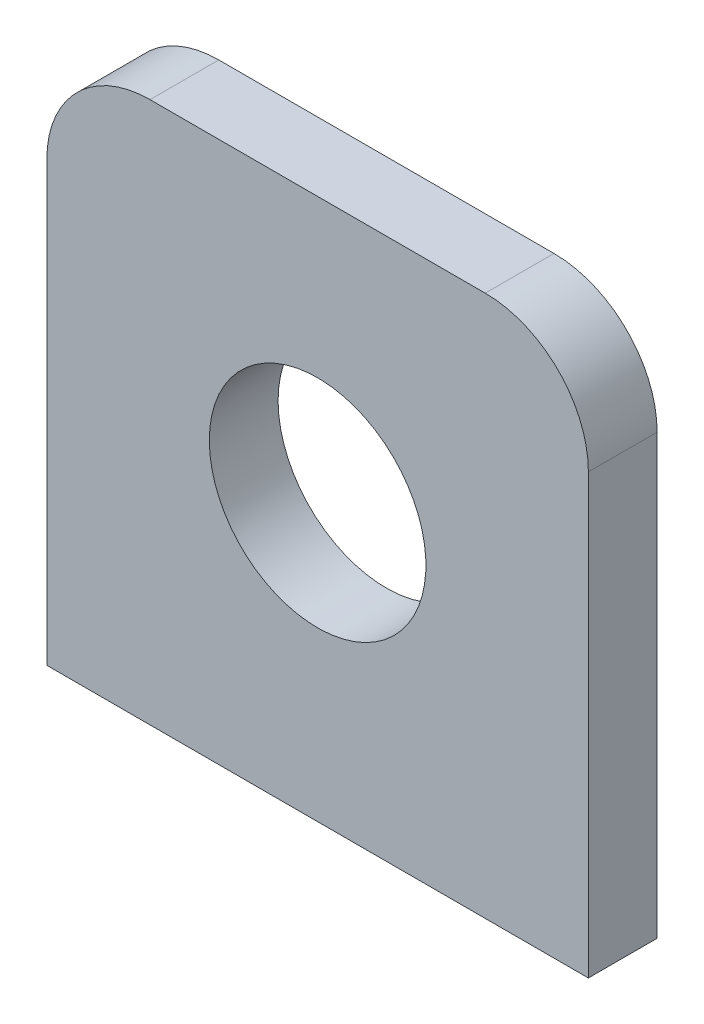
SolidWorks part; units mm, degrees
ref_plane "Plano frontal" through (0, 0, 0) normal (0, 0, 1) x (1, 0, 0)
ref_plane "Plano superior" through (0, 0, 0) normal (0, 1, 0) x (1, 0, 0)
ref_plane "Plano direito" through (0, 0, 0) normal (1, 0, 0) x (0, 0, -1)
ref_plane "Plano1" through (0, 0, 6.35) normal (0, 0, 1) x (1, 0, 0)
sketch "Esboço1" plane through (0, 0, 6.35) normal (0, 0, 1) x (1, 0, 0)
  line L0 (37, 0) -> (37, 50)
  line L1 (37, 50) -> (-13, 50)
  line L2 (-13, 50) -> (-13, 0)
  line L3 (-13, 0) -> (37, 0)
  dimension "D1" = 50
  dimension "D2" = 50
extrude "Ressalto-extrusão1" add sketch "Esboço1" against normal blind 6.35
hole_wizard "Furo com folga de M131" positions "Esboço5" profile "Esboço4" hole size "M13" standard "Ansi Metric" end condition through all
sketch "Esboço5" plane through (0, 0, 0) normal (0, 0, -1) x (-1, 0, 0)
  point P0 (-12, 25.5)
sketch "Esboço4" plane through (12, 25.5, 0) normal (1, 0, 0) x (0, 1, 0)
  line L0 (0, 0) -> (0, 6.35)
  line L1 (0, 6.35) -> (10, 6.35)
  line L2 (10, 6.35) -> (10, 0)
  line L5 (10, 0) -> (0, 0)
  line L11 (0, -6.35) -> (0, 107.95) construction
  dimension "Thru Hole Dia." = 20
  dimension "Thru Hole Depth" = 6.35
hole_wizard "Furo de diâmetro Ø3.3 (3.3)2" positions "Esboço7" profile "Esboço6" hole size "Ø3.3" standard "Ansi Metric"
sketch "Esboço7" plane through (0, 0, 0) normal (0, -1, 0) x (-1, 0, 0)
  point P0 (5.5, -3.175)
  point P1 (-29.5, -3.175)
  point P2 (0, 0)
  point P3 (0, 0)
sketch "Esboço6" plane through (-5.5, 0, 3.175) normal (1, 0, 0) x (0, 0, -1)
  line L0 (0, 0) -> (0, 10.0914)
  line L1 (0, 10.0914) -> (1.65, 9.1)
  line L2 (1.65, 9.1) -> (1.65, 0)
  line L5 (1.65, 0) -> (0, 0)
  line L10 (0, 10.0914) -> (-1.65, 9.1) construction
  line L11 (0, -6.35) -> (0, 107.95) construction
  dimension "Hole Dia." = 3.3
  dimension "Hole Depth" = 9.1
  dimension "Drill Angle" = 118
fillet "Filete1" radius 9.525 2 edges at (-13, 50, 3.175) (37, 50, 3.175)
